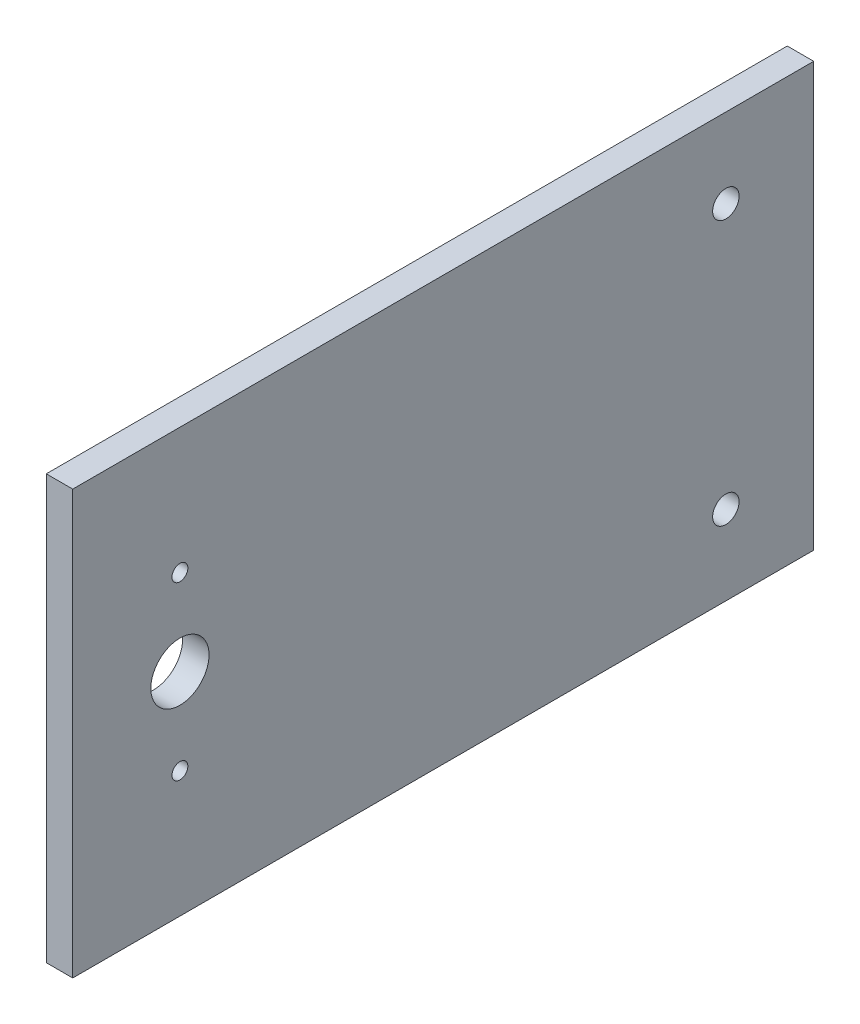
SolidWorks part; units mm, degrees
ref_plane "Front Plane" through (0, 0, 0) normal (1, 0, 0) x (0, 1, 0)
ref_plane "Top Plane" through (0, 0, 0) normal (0, 0, 1) x (0, 1, 0)
ref_plane "Right Plane" through (0, 0, 0) normal (0, 1, 0) x (-1, 0, 0)
sketch "Sketch1" plane through (0, 0, 0) normal (1, 0, 0) x (0, 1, 0)
  line L0 (0, 70) -> (0, -70) construction
  line L1 (-40, -70) -> (40, -70)
  line L2 (-40, -70) -> (-40, 70)
  line L3 (-40, 70) -> (40, 70)
  line L4 (40, -70) -> (40, 70)
  line L5 (-40, -70) -> (40, 70) construction
  line L6 (-40, 70) -> (40, -70) construction
  line L7 (-40, 49.75) -> (40, 49.75) construction
  line L9 (-25, -53.4) -> (25, -53.4) construction
  line L10 (-25, -53.4) -> (-25, 53.4) construction
  line L11 (-25, 53.4) -> (25, 53.4) construction
  line L12 (25, -53.4) -> (25, 53.4) construction
  line L13 (-25, -53.4) -> (25, 53.4) construction
  line L14 (-25, 53.4) -> (25, -53.4) construction
  circle A5 centre (0, 49.75) radius 5.5
  circle A6 centre (-16.22, 49.75) radius 1.5
  circle A7 centre (16.22, 49.75) radius 1.5
  circle A8 centre (-25, -53.4) radius 2.5
  circle A9 centre (25, -53.4) radius 2.5
  point P0 (0, 0)
  point P14 (0, 0)
  dimension "D5" = 16.22
  dimension "D6" = 16.6
  dimension "D7" = 50
  dimension "D8" = 11
  dimension "D4" = 3
  dimension "D9" = 5
  dimension "D10" = 5
  dimension "D1" = 80
  dimension "D2" = 140
  dimension "D3" = 119.75
extrude "Boss-Extrude1" add sketch "Sketch1" along normal blind 5
